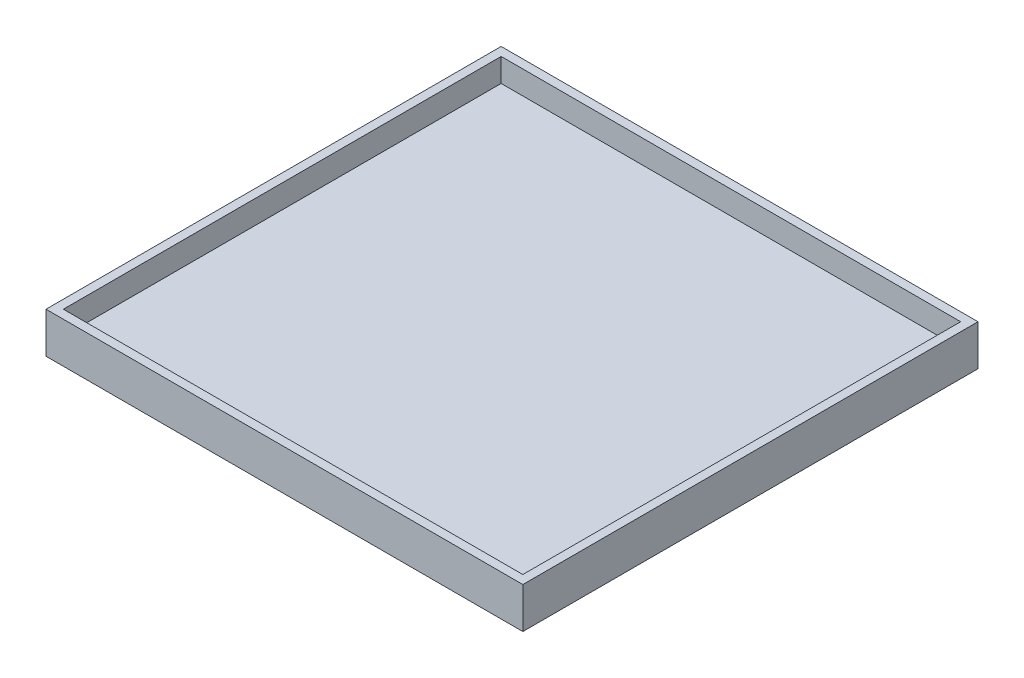
SolidWorks part; units mm, degrees
ref_plane "Front Plane" through (0, 0, 0) normal (0, 0, 1) x (1, 0, 0)
ref_plane "Top Plane" through (0, 0, 0) normal (0, 1, 0) x (1, 0, 0)
ref_plane "Right Plane" through (0, 0, 0) normal (1, 0, 0) x (0, 0, -1)
sketch "Sketch1" plane through (0, 0, 0) normal (0, 1, 0) x (1, 0, 0)
  line L0 (-53, 50.5) -> (53, 50.5)
  line L1 (-55, 52.5) -> (55, 52.5)
  line L2 (-55, 52.5) -> (-55, -52.5)
  line L3 (-55, -52.5) -> (55, -52.5)
  line L4 (55, 52.5) -> (55, -52.5)
  line L5 (-55, 52.5) -> (55, -52.5) construction
  line L6 (-55, -52.5) -> (55, 52.5) construction
  line L7 (53, 50.5) -> (53, -50.5)
  line L8 (-53, -50.5) -> (53, -50.5)
  line L9 (-53, 50.5) -> (-53, -50.5)
  point P0 (0, 0)
  dimension "D1" = 2
extrude "Boss-Extrude1" add sketch "Sketch1" against normal blind 5.4
sketch "Sketch2" plane through (0, -5.4, 0) normal (0, -1, 0) x (1, 0, 0)
  line L1 (-55, 52.5) -> (55, 52.5)
  line L2 (-55, 52.5) -> (-55, -52.5)
  line L3 (-55, -52.5) -> (55, -52.5)
  line L4 (55, 52.5) -> (55, -52.5)
extrude "Boss-Extrude2" add sketch "Sketch2" along normal blind 4
